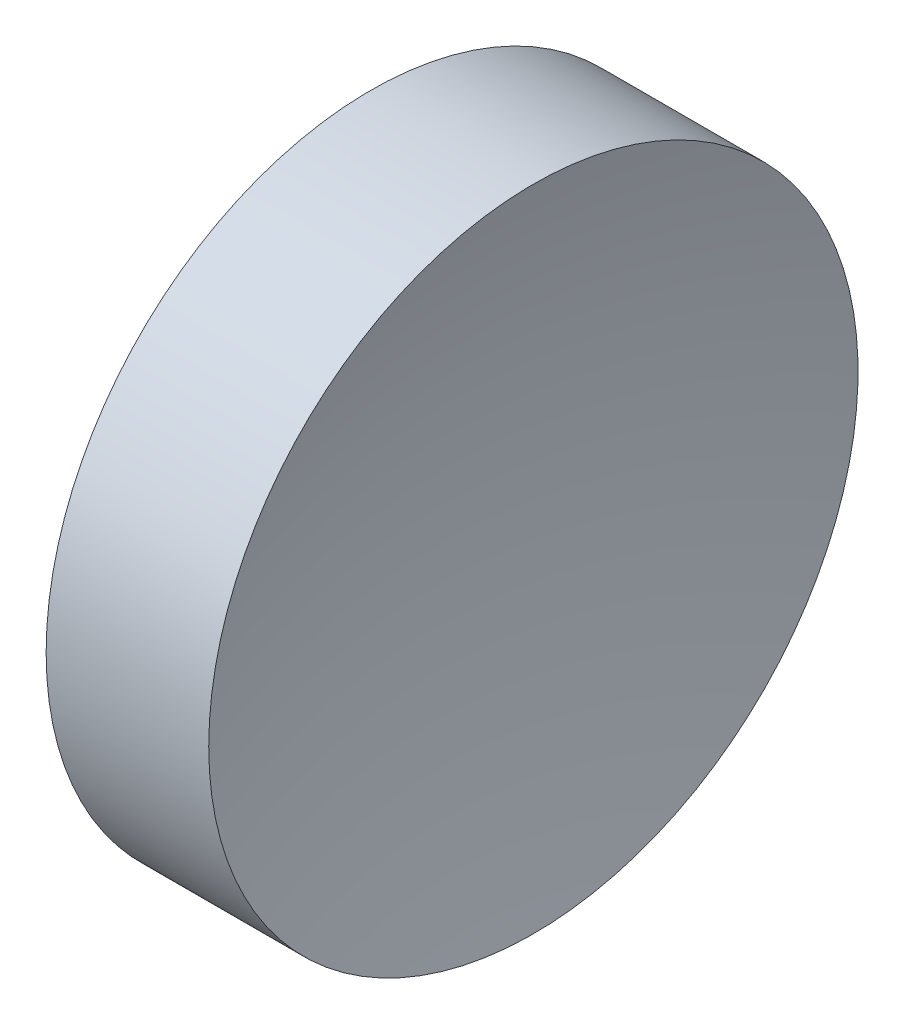
SolidWorks part; units mm, degrees
ref_plane "前视基准面" through (0, 0, 0) normal (0, 0, 1) x (1, 0, 0)
ref_plane "上视基准面" through (0, 0, 0) normal (0, 1, 0) x (1, 0, 0)
ref_plane "右视基准面" through (0, 0, 0) normal (1, 0, 0) x (0, 0, -1)
sketch "草图1" plane through (0, 0, 0) normal (0, 1, 0) x (1, 0, 0)
  line L0 (0, 0) -> (6.9328, 0) construction
  line L1 (0, 0) -> (2.36, 0)
  line L2 (0, 0) -> (0, 6.35)
  line L3 (0, 6.35) -> (3.1799, 6.35)
  arc A0 (3.1799, 6.35) -> (2.36, 0) centre (27.36, 0) ccw
  dimension "D3" = 25
  dimension "D1" = 2.36
  dimension "D2" = 6.35
revolve "旋转1" add sketch "草图1" angle 360 about L0
